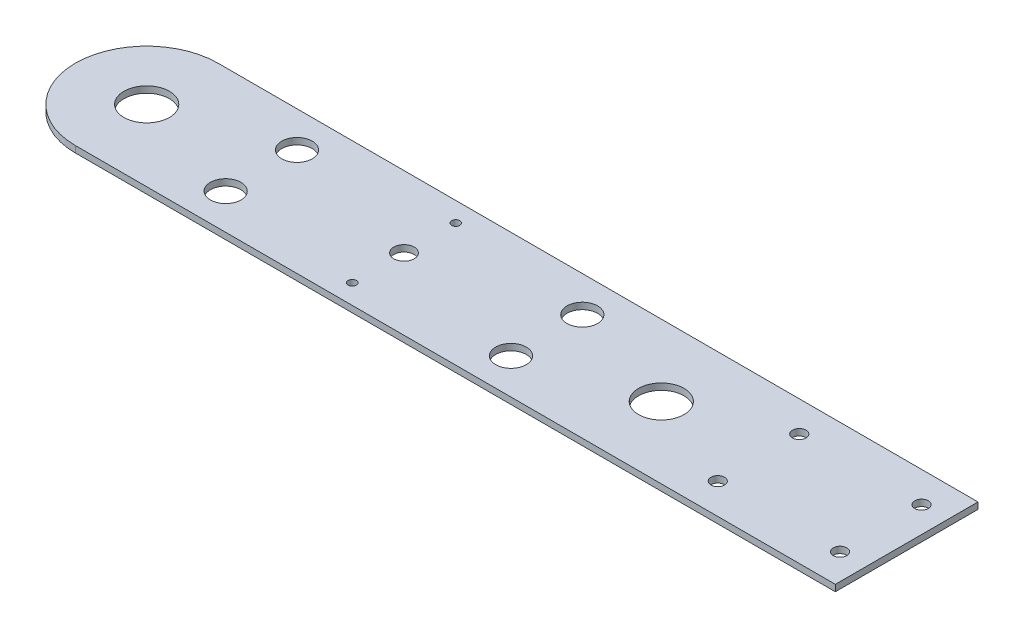
SolidWorks part; units mm, degrees
ref_plane "Front Plane" through (0, 0, 0) normal (0, 0, 1) x (1, 0, 0)
ref_plane "Top Plane" through (0, 0, 0) normal (0, 1, 0) x (1, 0, 0)
ref_plane "Right Plane" through (0, 0, 0) normal (1, 0, 0) x (0, 0, -1)
sketch "Sketch1" plane through (0, 0, 0) normal (0, 1, 0) x (1, 0, 0)
  line L0 (126.2582, 0) -> (-126.2582, 0)
  line L1 (-126.2582, 35) -> (126.2582, 35)
  line L3 (-126.2582, -35) -> (126.2582, -35)
  line L4 (-70, 35) -> (-70, 0) construction
  line L5 (-70, 0) -> (-70, -35) construction
  line L6 (70, 35) -> (70, 0) construction
  line L7 (70, 0) -> (70, -35) construction
  line L8 (0, -35) -> (0, 35) construction
  line L9 (161.2582, -35) -> (161.2582, 35) construction
  line L10 (161.2582, -35) -> (126.2582, -35)
  line L11 (161.2582, 35) -> (126.2582, 35)
  line L12 (246.6582, 0) -> (161.2582, 0) construction
  line L13 (161.2582, -35) -> (246.6582, -35)
  line L15 (161.2582, 35) -> (246.6582, 35)
  line L16 (246.6582, -35) -> (246.6582, 35)
  line L17 (203.9582, 20) -> (203.9582, -20) construction
  line L18 (161.2582, 20) -> (246.6582, 20) construction
  line L19 (161.2582, -20) -> (246.6582, -20) construction
  circle A0 centre (-126.2582, 0) radius 35
  circle A2 centre (-126.2582, 0) radius 11.15
  circle A3 centre (126.2582, 0) radius 11.15
  circle A5 centre (-70, -17.5) radius 7.5
  circle A6 centre (-70, 17.5) radius 7.5
  circle A7 centre (70, 17.5) radius 7.5
  circle A8 centre (70, -17.5) radius 7.5
  circle A9 centre (0, 0) radius 5
  circle A10 centre (0, -25.4) radius 2.02
  circle A11 centre (0, 25.4) radius 2.02
  circle A14 centre (233.9582, -20) radius 3.325
  circle A15 centre (173.9582, -20) radius 3.325
  circle A16 centre (173.9582, 20) radius 3.325
  circle A17 centre (233.9582, 20) radius 3.325
  point P4 (0, 0)
  point P38 (161.2582, 0)
  point P39 (-161.2582, 0)
  point P45 (203.9582, 0)
  point P48 (203.9582, 20)
  point P53 (203.9582, -20)
  dimension "D1" = 22.3
  dimension "D2" = 10
  dimension "D3" = 70
  dimension "D4" = 15
  dimension "D7" = 25.4
  dimension "D8" = 25.4
  dimension "D9" = 4.04
  dimension "D10" = 4.04
  dimension "D13" = 6.65
  dimension "D5" = 70
  dimension "D6" = 70
  dimension "D11" = 40
  dimension "D12" = 322.5164
  dimension "D14" = 60
  dimension "D15" = 60
  dimension "D16" = 12.7
  dimension "D17" = 12.7
  dimension "D18" = 12.7
extrude "Boss-Extrude1" add sketch "Sketch1" along normal blind 3.175
